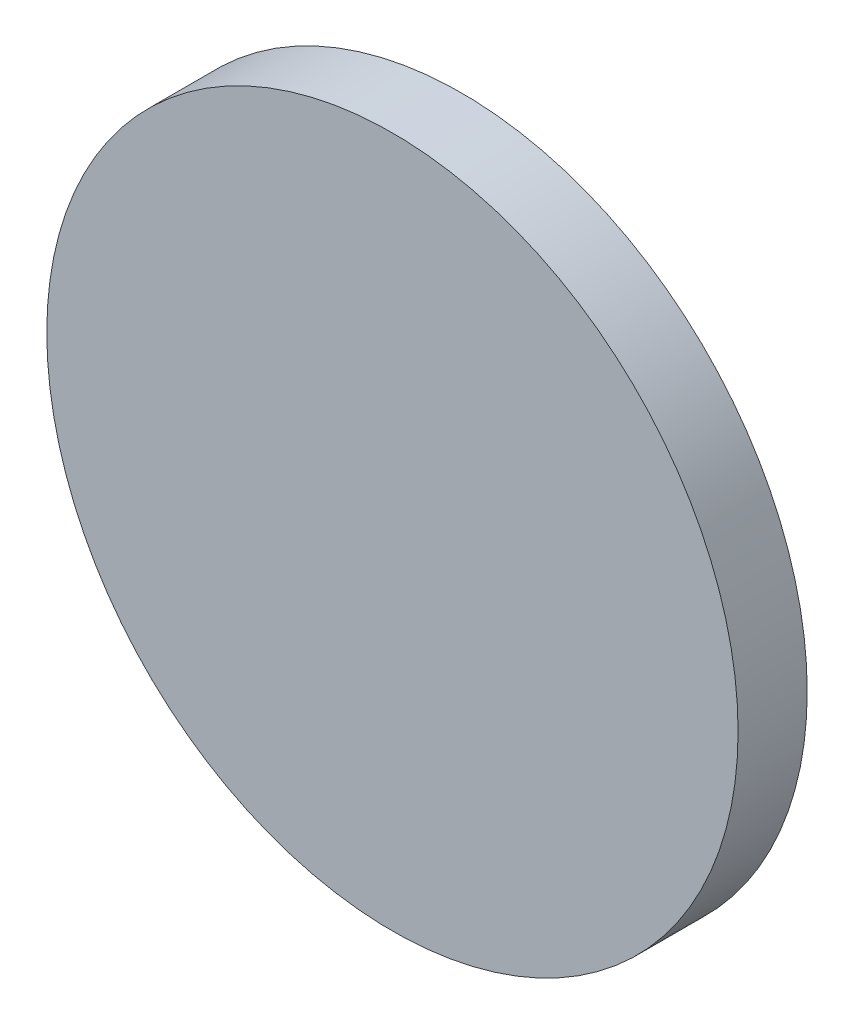
SolidWorks part; units mm, degrees
ref_plane "Front Plane" through (0, 0, 0) normal (0, 0, 1) x (1, 0, 0)
ref_plane "Top Plane" through (0, 0, 0) normal (0, 1, 0) x (1, 0, 0)
ref_plane "Right Plane" through (0, 0, 0) normal (1, 0, 0) x (0, 0, -1)
sketch "Sketch3" plane through (0, 0, 0) normal (0, 0, 1) x (1, 0, 0)
  circle A0 centre (0, 0) radius 31.75
extrude "Boss-Extrude2" add sketch "Sketch3" along normal blind 6.35
sketch "Sketch4" plane through (0, 0, 0) normal (0, 0, 1) x (1, 0, 0)
  line L0 (-31.75, 0) -> (31.75, 0)
  line L3 (0, -31.75) -> (0, 31.75)
  line L6 (6.1011, -12.941) -> (6.1011, 12.941)
  line L7 (-11.491, -10.0831) -> (-11.491, 10.0831)
  line L8 (-11.491, 10.0831) -> (-11.491, 0)
  line L9 (-11.491, 0) -> (-11.491, -10.0831)
  line L10 (-11.491, 0) -> (-11.491, 10.0831)
  line L11 (-7.6663, -12.3498) -> (-7.3296, 12.4908)
  line L12 (-7.4679, 2.2902) -> (-5.1777, 0)
  line L13 (-5.1777, 0) -> (-7.5308, -2.3531)
  line L14 (19.6532, 0) -> (19.6532, 15.494)
  line L15 (19.6532, 15.494) -> (19.6532, -15.494)
  line L16 (19.6532, -15.494) -> (19.6532, 0)
  line L17 (19.6532, -15.494) -> (19.6532, 0)
  line L18 (19.6532, 0) -> (19.6532, -15.494)
  line L19 (3.1453, 17.5998) -> (3.1453, 13.6542)
  line L20 (3.1453, -17.5998) -> (3.1453, -13.6542)
  line L21 (10.3047, 20.0808) -> (10.3047, 10.9368)
  line L22 (10.3365, -20.0599) -> (10.3365, -10.9159)
  circle A0 centre (-11.491, -5.0416) radius 1.143
  circle A1 centre (-11.491, 5.0416) radius 1.143
  circle A2 centre (19.6532, 7.747) radius 4.9623
  circle A3 centre (19.6532, -7.747) radius 4.8737
  ellipse E0 centre (0, 0) end of major axis (16.6899, 0) minor radius 13.9033
  ellipse E1 centre (6.1011, 0) end of major axis (15.1321, 0) minor radius 8.0476
  ellipse E2 centre (0, 0) end of major axis (18.157, 0) minor radius 15.5025
  ellipse E3 centre (3.1453, 17.5998) end of major axis (-4.0142, 15.1189) minor radius 3.0241
  ellipse E4 centre (3.1453, -17.5998) end of major axis (10.3365, -20.0599) minor radius 2.9995
  point P51 (3.1453, -17.5998)
  point P60 (10.3365, -20.0599)
  dimension "D1" = 2.286
  dimension "D2" = 2.286
  dimension "D3" = 15.494
  dimension "D4" = 15.494
  dimension "D5" = 3.9457
  dimension "D6" = 9.144
  dimension "D7" = 9.144
  dimension "D8" = 3.9457
extrude "Cut-Extrude1" cut sketch "Sketch4" along normal blind 2.54
sketch "Sketch8" plane through (0, 0, 0) normal (0, 0, -1) x (-1, 0, 0)
  line L0 (31.75, 0) -> (-31.75, 0)
  line L1 (19.5015, 25.055) -> (19.5015, -25.055)
  line L2 (27.3117, 12.4702) -> (19.9089, 12.4702)
  line L3 (19.9089, 12.4702) -> (19.7934, 11.0304)
  line L4 (19.7934, 11.0304) -> (19.5015, 11.0304)
  line L5 (19.5015, 11.0304) -> (19.5015, 14.9438)
  line L6 (19.5015, 14.9438) -> (19.7934, 14.9438)
  line L7 (19.7934, 14.9438) -> (19.9089, 13.5411)
  line L8 (19.9089, 13.5411) -> (26.7602, 13.5411)
  line L9 (26.7602, 13.5411) -> (26.5297, 14.9438)
  line L10 (26.5297, 14.9438) -> (26.827, 14.9438)
  line L11 (26.827, 14.9438) -> (27.3117, 12.4702)
  line L12 (27.3117, 6.0243) -> (19.8512, 6.0243)
  line L13 (19.8512, 6.0243) -> (19.8512, 4.5727)
  line L14 (19.8512, 4.5727) -> (19.5015, 4.5727)
  line L15 (19.5015, 4.5727) -> (19.5015, 8.4963)
  line L16 (19.5015, 8.4963) -> (19.7934, 8.4963)
  line L17 (19.7934, 8.4963) -> (19.8512, 7.09)
  line L18 (19.8512, 7.09) -> (26.7602, 7.09)
  line L19 (26.7602, 7.09) -> (26.5297, 8.4926)
  line L20 (26.5297, 8.4926) -> (26.827, 8.4926)
  line L21 (26.827, 8.4926) -> (27.3117, 6.0243)
  line L22 (21.6484, -1.5649) -> (21.6484, -2.5394)
  line L23 (21.6484, -2.5394) -> (22.4291, -2.5394)
  line L24 (22.4291, -2.5394) -> (22.4291, -1.5649)
  line L25 (22.4291, -1.5649) -> (27.3117, -1.562)
  line L26 (27.3117, -1.562) -> (27.3117, -0.9675)
  line L27 (27.3117, -0.9675) -> (22.173, 2.9274)
  line L28 (22.173, 2.9274) -> (21.6484, 2.9274)
  line L29 (21.6484, 2.9274) -> (21.6484, -0.6853)
  line L30 (21.6484, -0.6853) -> (19.9864, -0.646)
  line L31 (19.9864, -0.646) -> (19.7934, 0.3869)
  line L32 (19.7934, 0.3869) -> (19.5015, 0.3869)
  line L33 (19.5015, 0.3869) -> (19.5015, -2.5394)
  line L34 (19.5015, -2.5394) -> (19.7934, -2.5394)
  line L35 (19.7934, -2.5394) -> (19.9864, -1.6121)
  line L36 (19.9864, -1.6121) -> (21.6484, -1.5649)
  line L37 (26.4739, -0.6853) -> (22.4291, -0.6853)
  line L38 (22.4291, -0.6853) -> (22.4291, 2.3733)
  line L39 (22.4291, 2.3733) -> (26.4739, -0.6853)
  line L40 (19.5015, -4.4078) -> (20.8174, -4.4078)
  line L41 (20.8174, -4.4078) -> (20.8174, -4.8837)
  line L42 (20.8174, -4.8837) -> (19.7934, -4.9845)
  line L43 (19.7934, -4.9845) -> (19.6228, -5.8043)
  line L44 (23.7317, -5.8043) -> (23.8229, -4.5008)
  line L45 (23.8229, -4.5008) -> (27.1044, -4.5008)
  line L46 (27.1044, -4.5008) -> (27.1044, -8.487)
  line L47 (27.1044, -8.487) -> (26.2391, -8.487)
  line L48 (26.2391, -8.487) -> (26.2391, -4.7953)
  line L49 (26.2391, -4.7953) -> (24.0832, -4.7953)
  line L50 (24.0832, -4.7953) -> (24.0832, -6.2867)
  line L51 (19.3115, -6.2867) -> (19.5015, -4.4078)
  line L52 (22.4291, -14.4837) -> (22.4291, -15.4239)
  line L53 (22.4291, -15.4239) -> (21.6973, -15.4239)
  line L54 (21.6973, -15.4239) -> (21.6484, -15.4239)
  line L55 (21.6484, -15.4239) -> (21.6484, -14.4467)
  line L56 (21.6484, -14.4467) -> (19.9864, -14.4467)
  line L57 (19.9864, -14.4467) -> (19.7815, -15.4239)
  line L58 (19.7815, -15.4239) -> (19.5015, -15.4239)
  line L59 (19.5015, -15.4239) -> (19.5015, -12.4792)
  line L60 (19.5015, -12.4792) -> (19.7815, -12.4792)
  line L61 (19.7815, -12.4792) -> (19.9864, -13.5056)
  line L62 (19.9864, -13.5056) -> (21.6484, -13.5718)
  line L63 (21.6484, -13.5718) -> (21.6484, -9.9598)
  line L64 (21.6484, -9.9598) -> (22.173, -9.9598)
  line L65 (22.173, -9.9598) -> (27.3117, -13.8478)
  line L66 (27.3117, -13.8478) -> (27.3117, -14.4837)
  line L67 (27.3117, -14.4837) -> (22.4291, -14.4837)
  line L68 (22.4291, -13.5718) -> (26.4739, -13.5718)
  line L69 (26.4739, -13.5718) -> (22.4291, -10.5115)
  line L70 (22.4291, -10.5115) -> (22.4291, -13.5718)
  circle A0 centre (0, 0) radius 31.75 construction
  arc A1 (19.6228, -5.8043) -> (23.7317, -5.8043) centre (21.6772, -5.4802) ccw
  arc A2 (24.0832, -6.2867) -> (19.3115, -6.2867) centre (21.6973, -6.2867) cw
  text T0 "11454" font "Lucida Bright" height in points 28
extrude "Cut-Extrude2" cut sketch "Sketch8" against normal blind 2.54 contours L8 L9 L10 L11 L2 L3 L4 L5 L6 L7 | L18 L19 L20 L21 L12 L13 L14 L15 L16 L17 | L29 L30 L31 L32 L33 L34 L35 L36 L22 L23 L24 L25 L26 L27 L28 | L38 L39 L37 | A2 L51 L40 L41 L42 L43 A1 L44 L45 L46 L47 L48 L49 L50 | L63 L64 L65 L66 L67 L52 L53 L54 L55 L56 L57 L58 L59 L60 L61 L62 | L70 L68 L69
